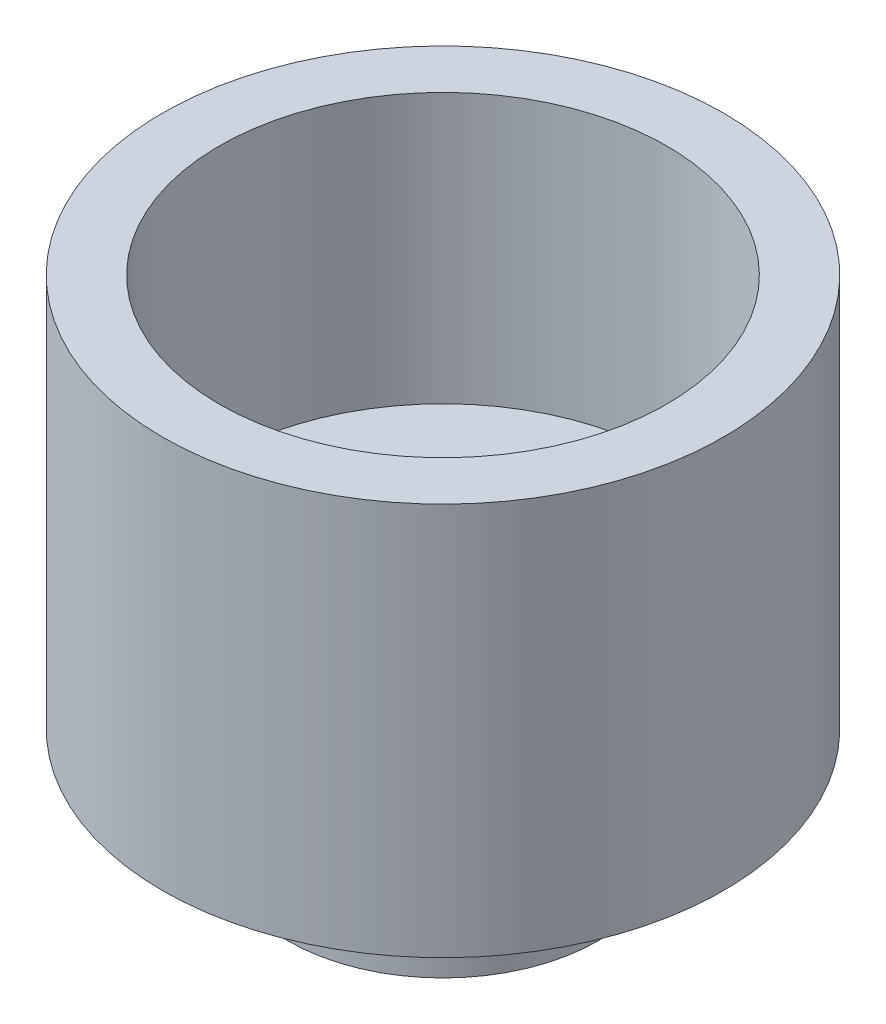
SolidWorks part; units mm, degrees
ref_plane "Plan de face" through (0, 0, 0) normal (0, 0, 1) x (1, 0, 0)
ref_plane "Plan de dessus" through (0, 0, 0) normal (0, 1, 0) x (1, 0, 0)
ref_plane "Plan de droite" through (0, 0, 0) normal (1, 0, 0) x (0, 0, -1)
sketch "Esquisse1" plane through (0, 0, 0) normal (0, 1, 0) x (1, 0, 0)
  circle A0 centre (0, 0) radius 9.5
  dimension "D1" = 19
extrude "Boss.-Extru.2" add sketch "Esquisse1" along normal blind 13.3 contours A0
sketch "Esquisse3" plane through (0, 0, 0) normal (0, -1, 0) x (1, 0, 0)
  circle A0 centre (0, 0) radius 5.25
  dimension "D1" = 10.5
extrude "Boss.-Extru.3" add sketch "Esquisse3" along normal blind 3.6
sketch "Esquisse4" plane through (0, 13.3, 0) normal (0, 1, 0) x (1, 0, 0)
  circle A0 centre (0, 0) radius 7.575
  dimension "D1" = 15.15
extrude "Enlèv. mat.-Extru.1" cut sketch "Esquisse4" against normal blind 9.13 contours A0
sketch "Esquisse5" plane through (0, -3.6, 0) normal (0, -1, 0) x (1, 0, 0)
  circle A0 centre (0, 0) radius 1.575
  dimension "D1" = 3.15
extrude "Enlèv. mat.-Extru.2" cut sketch "Esquisse5" against normal blind 9.13
